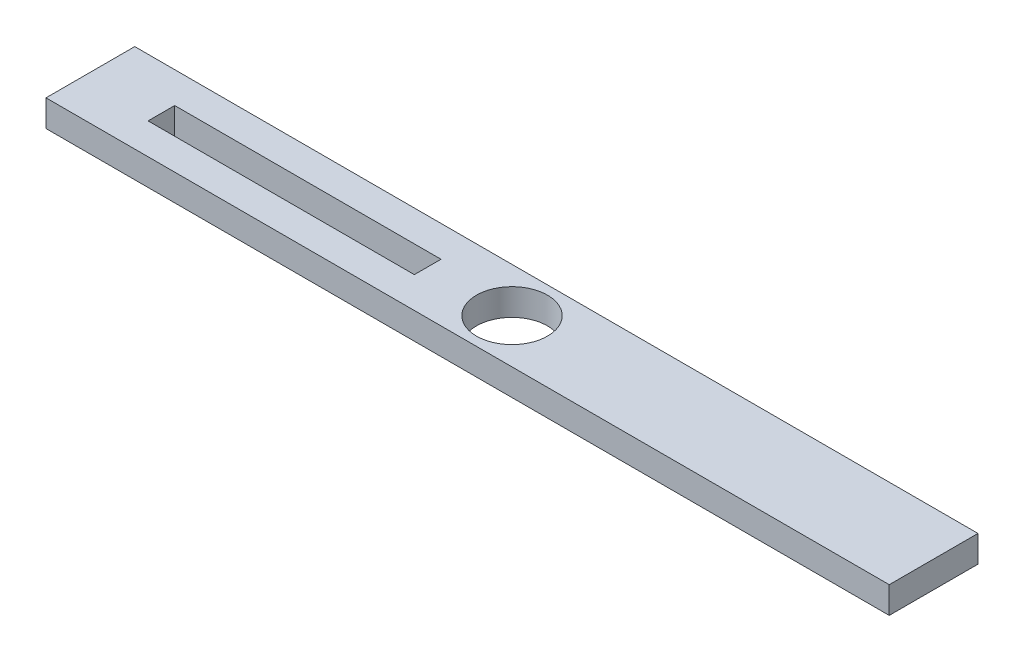
SolidWorks part; units mm, degrees
ref_plane "Alzado" through (0, 0, 0) normal (0, 0, 1) x (1, 0, 0)
ref_plane "Planta" through (0, 0, 0) normal (0, 1, 0) x (1, 0, 0)
ref_plane "Vista lateral" through (0, 0, 0) normal (1, 0, 0) x (0, 0, -1)
sketch "Croquis1" plane through (0, 0, 0) normal (0, 1, 0) x (1, 0, 0)
  line L1 (-47.5, -5) -> (47.5, -5)
  line L2 (-47.5, -5) -> (-47.5, 5)
  line L3 (-47.5, 5) -> (47.5, 5)
  line L4 (47.5, -5) -> (47.5, 5)
  line L5 (-47.5, -5) -> (47.5, 5) construction
  line L6 (-47.5, 5) -> (47.5, -5) construction
  line L7 (-39.5, -1.5) -> (-9.5, -1.5)
  line L8 (-39.5, -1.5) -> (-39.5, 1.5)
  line L9 (-39.5, 1.5) -> (-9.5, 1.5)
  line L10 (-9.5, -1.5) -> (-9.5, 1.5)
  line L11 (-39.5, -1.5) -> (-9.5, 1.5) construction
  line L12 (-39.5, 1.5) -> (-9.5, -1.5) construction
  circle A0 centre (0, 0) radius 4
  point P0 (0, 0)
  point P8 (-24.5, 0)
  point P13 (0, 0)
  point P14 (0, 0)
  dimension "D3" = 8
  dimension "D4" = 9.5
  dimension "D1" = 10
  dimension "D2" = 95
  dimension "D5" = 30
  dimension "D6" = 3
extrude "Saliente-Extruir1" add sketch "Croquis1" along normal blind 3
